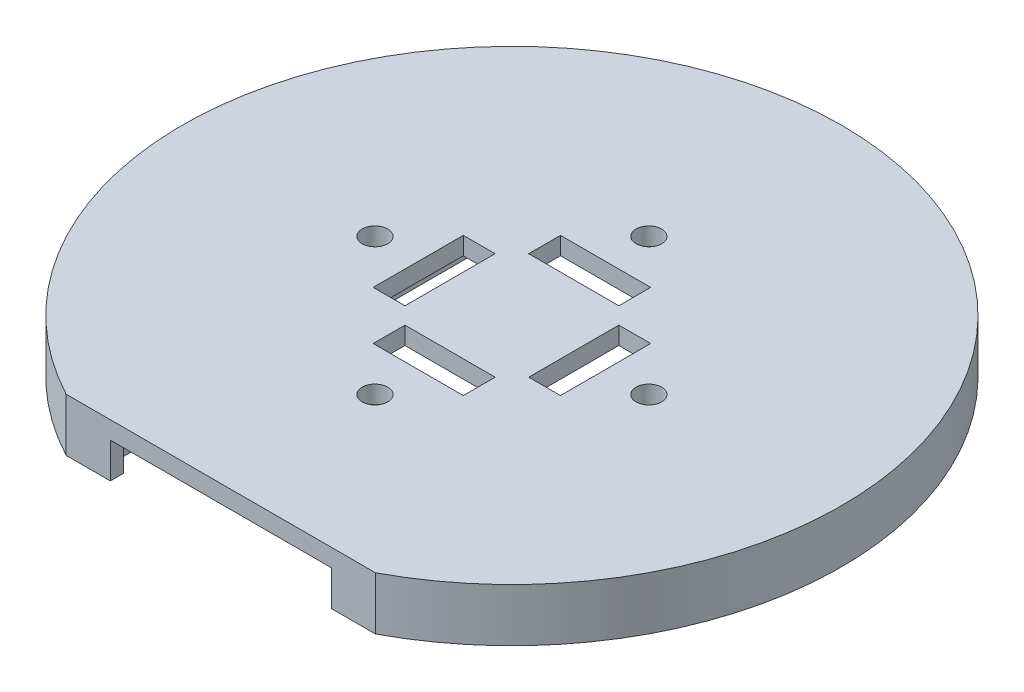
SolidWorks part; units mm, degrees
ref_plane "Front Plane" through (0, 0, 0) normal (0, 0, 1) x (1, 0, 0)
ref_plane "Top Plane" through (0, 0, 0) normal (0, 1, 0) x (1, 0, 0)
ref_plane "Right Plane" through (0, 0, 0) normal (1, 0, 0) x (0, 0, -1)
sketch "Sketch1" plane through (0, 0, 0) normal (0, 1, 0) x (1, 0, 0)
  line L0 (-17.5, -32.9399) -> (17.5, -32.9399)
  arc A0 (17.5, -32.9399) -> (-17.5, -32.9399) centre (0, 0) ccw
  dimension "D1" = 74.6
  dimension "D2" = 35
extrude "Boss-Extrude1" add sketch "Sketch1" along normal blind 6
sketch "Sketch2" plane through (0, 0, 0) normal (0, -1, 0) x (1, 0, 0)
  line L0 (-17.5, 32.9399) -> (17.5, 32.9399) construction
  line L5 (-14.15, 31.4399) -> (14.15, 31.4399)
  line L6 (-14.15, 31.4399) -> (-14.15, -32.8601)
  line L7 (-14.15, -32.8601) -> (14.15, -32.8601)
  line L8 (14.15, 31.4399) -> (14.15, -32.8601)
  line L9 (-14.15, 31.4399) -> (14.15, -32.8601) construction
  line L10 (-14.15, -32.8601) -> (14.15, 31.4399) construction
  point P0 (0, -0.7101)
  point P5 (0, 9.7483)
  dimension "D1" = 1.5
  dimension "D2" = 64.3
  dimension "D3" = 28.3
extrude "Cut-Extrude1" cut sketch "Sketch2" against normal blind 4
sketch "Sketch3" plane through (0, 6, 0) normal (0, 1, 0) x (1, 0, 0)
  line L1 (-5.1, 10.6) -> (5.1, 10.6)
  line L2 (-5.1, 10.6) -> (-5.1, 7)
  line L3 (-5.1, 7) -> (5.1, 7)
  line L4 (5.1, 10.6) -> (5.1, 7)
  line L5 (-5.1, 10.6) -> (5.1, 7) construction
  line L6 (-5.1, 7) -> (5.1, 10.6) construction
  circle A0 centre (0, 15.5) radius 1.45
  point P0 (0, 8.8)
  point P7 (0, 0)
  dimension "D1" = 2.9
  dimension "D2" = 15.5
  dimension "D3" = 7
  dimension "D4" = 10.2
  dimension "D5" = 3.6
extrude "Cut-Extrude2" cut sketch "Sketch3" against normal through all
pattern_circular "CirPattern1" count 4 over 360 about axis through (0, 0, 0) along (0, 1, 0) of "Cut-Extrude2"
sketch "Sketch4" plane through (0, 0, 32.9399) normal (0, 0, 1) x (1, 0, 0)
  line L0 (-17.5, 0) -> (17.5, 0) construction
  line L1 (-12.5, 0) -> (12.5, 0)
  line L2 (-12.5, 0) -> (-12.5, 4)
  line L3 (-12.5, 4) -> (12.5, 4)
  line L4 (12.5, 0) -> (12.5, 4)
  line L5 (14.15, 4) -> (-14.15, 4) construction
  point P9 (0, 0)
  dimension "D1" = 25
extrude "Cut-Extrude3" cut sketch "Sketch4" against normal up to next
